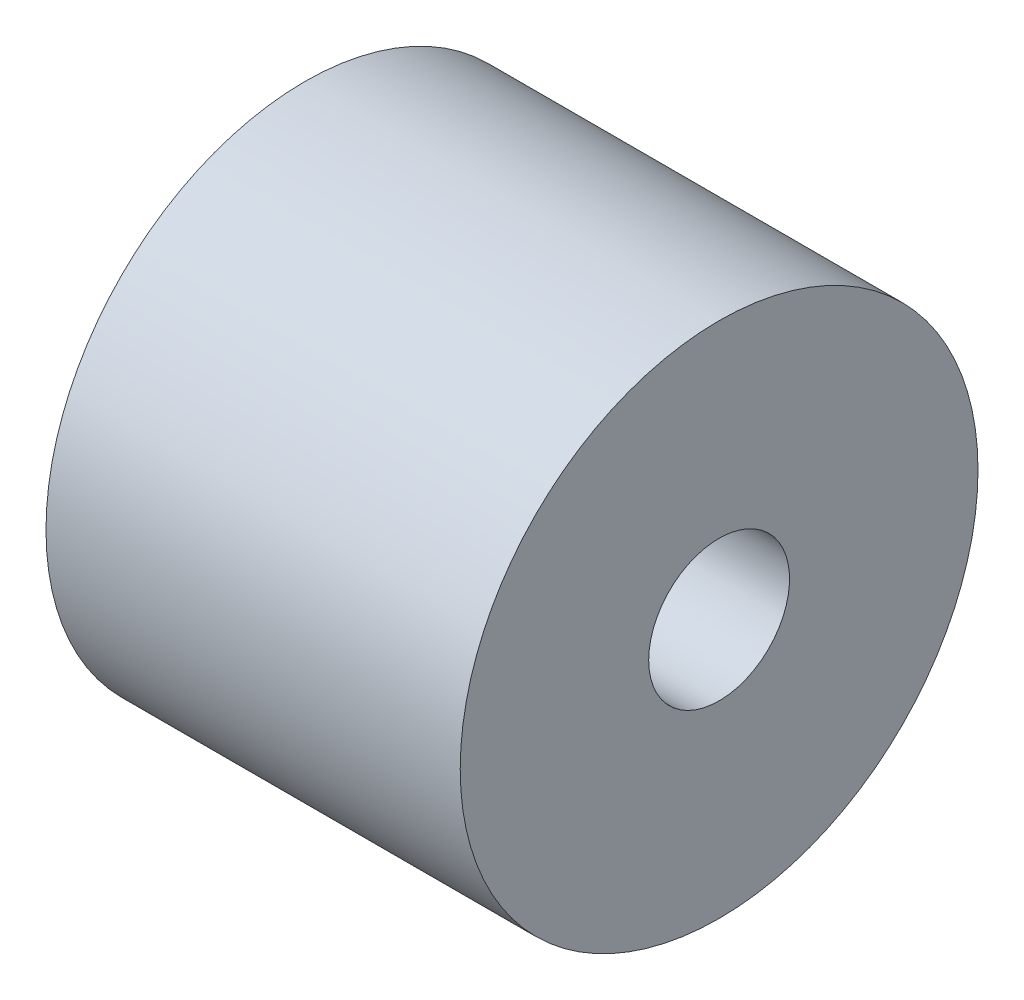
SolidWorks part; units mm, degrees
material "AISI 1020"
ref_plane "Спереди" through (0, 0, 0) normal (0, 0, 1) x (1, 0, 0)
ref_plane "Сверху" through (0, 0, 0) normal (0, 1, 0) x (1, 0, 0)
ref_plane "Справа" through (0, 0, 0) normal (1, 0, 0) x (0, 0, -1)
sketch "Эскиз1" plane through (0, 0, 0) normal (0, 0, 1) x (1, 0, 0)
  line L0 (-1000, 0) -> (49000, 0) construction
  line L1 (0, 0) -> (0, 12.5)
  line L2 (0, 12.5) -> (-20, 12.5)
  line L3 (-20, 12.5) -> (-20, 0)
  line L4 (-20, 0) -> (0, 0)
  dimension "D1" = 20
revolve "Повернуть1" add sketch "Эскиз1" angle 360 about L0
hole_wizard "Отверстие обработанное метчиком M81" positions "Эскиз2" profile "Эскиз3" tap size "M8" standard "ISO" end condition through all
sketch "Эскиз2" plane through (-20, 0, 0) normal (-1, 0, 0) x (0, 0, 1)
  point P0 (0, 0)
sketch "Эскиз3" plane through (-20, 0, 0) normal (0, 1, 0) x (0, 0, 1)
  line L0 (0, 0) -> (0, 20)
  line L1 (0, 20) -> (3.4, 20)
  line L2 (3.4, 20) -> (3.4, 0)
  line L5 (3.4, 0) -> (0, 0)
  line L11 (0, -6.35) -> (0, 107.95) construction
  dimension "Диаметр проходного сверла" = 6.8
  dimension "Глубина проходного сверла" = 20
cosmetic thread "Отверстие резьбы1" parameters "D2"=8
